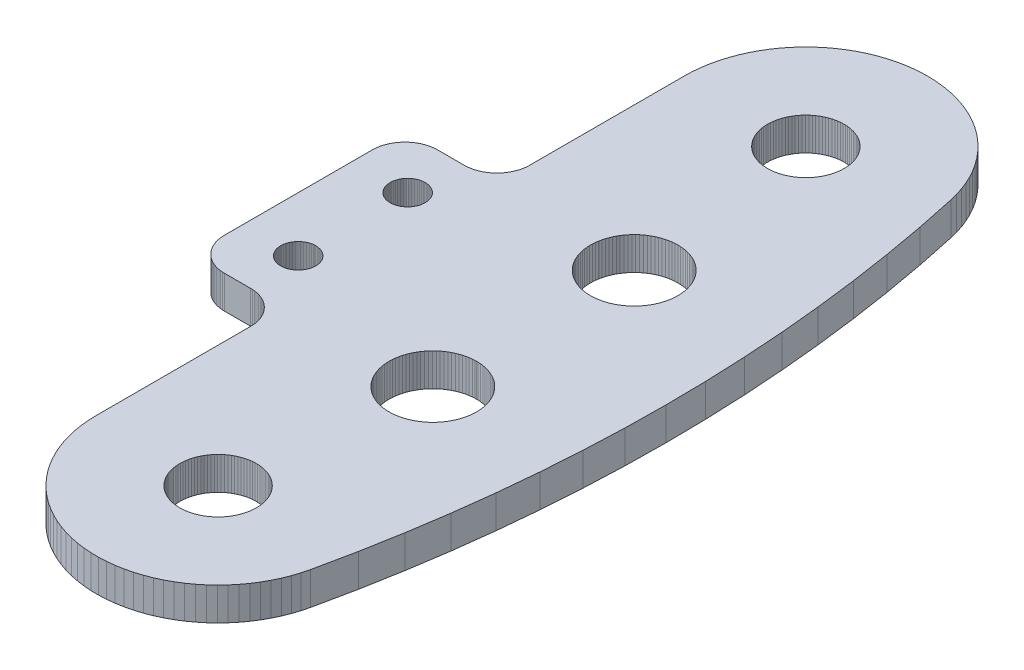
SolidWorks part; units mm, degrees
ref_plane "Front Plane" through (0, 0, 0) normal (0, 0, 1) x (1, 0, 0)
ref_plane "Top Plane" through (0, 0, 0) normal (0, 1, 0) x (1, 0, 0)
ref_plane "Right Plane" through (0, 0, 0) normal (1, 0, 0) x (0, 0, -1)
ref_plane "Plane1" through (0, 3, 0) normal (0, 1, 0) x (1, 0, 0)
sketch "Sketch1" plane through (0, 3, 0) normal (0, 1, 0) x (1, 0, 0)
  line L0 (19.864, -7.6394) -> (20.0843, -7.6675)
  line L1 (20.0843, -7.6675) -> (20.3023, -7.7095)
  line L2 (20.3023, -7.7095) -> (20.5173, -7.7653)
  line L3 (20.5173, -7.7653) -> (20.7283, -7.8346)
  line L4 (20.7283, -7.8346) -> (20.9345, -7.9171)
  line L5 (20.9345, -7.9171) -> (21.1351, -8.0126)
  line L6 (21.1351, -8.0126) -> (21.3291, -8.1206)
  line L7 (21.3291, -8.1206) -> (21.516, -8.2407)
  line L8 (21.516, -8.2407) -> (21.6948, -8.3723)
  line L9 (21.6948, -8.3723) -> (21.865, -8.5151)
  line L10 (21.865, -8.5151) -> (22.0257, -8.6684)
  line L11 (22.0257, -8.6684) -> (22.1764, -8.8315)
  line L12 (22.1764, -8.8315) -> (22.3164, -9.0039)
  line L13 (22.3164, -9.0039) -> (22.4453, -9.1848)
  line L14 (22.4453, -9.1848) -> (22.5623, -9.3735)
  line L15 (22.5623, -9.3735) -> (22.6672, -9.5693)
  line L16 (22.6672, -9.5693) -> (22.7595, -9.7713)
  line L17 (22.7595, -9.7713) -> (22.8388, -9.9788)
  line L18 (22.8388, -9.9788) -> (22.9047, -10.1909)
  line L19 (22.9047, -10.1909) -> (22.9571, -10.4067)
  line L20 (22.9571, -10.4067) -> (22.9956, -10.6254)
  line L21 (22.9956, -10.6254) -> (23.0203, -10.8461)
  line L22 (23.0203, -10.8461) -> (23.0308, -11.068)
  line L23 (23.0308, -11.068) -> (23.0273, -11.2901)
  line L24 (23.0273, -11.2901) -> (23.0097, -11.5115)
  line L25 (23.0097, -11.5115) -> (22.9781, -11.7314)
  line L26 (22.9781, -11.7314) -> (22.9326, -11.9487)
  line L27 (22.9326, -11.9487) -> (22.8734, -12.1628)
  line L28 (22.8734, -12.1628) -> (22.8008, -12.3727)
  line L29 (22.8008, -12.3727) -> (22.715, -12.5775)
  line L30 (22.715, -12.5775) -> (22.6164, -12.7765)
  line L31 (22.6164, -12.7765) -> (22.5053, -12.9689)
  line L32 (22.5053, -12.9689) -> (22.3823, -13.1538)
  line L33 (22.3823, -13.1538) -> (22.2478, -13.3305)
  line L34 (22.2478, -13.3305) -> (22.1023, -13.4984)
  line L35 (22.1023, -13.4984) -> (21.9466, -13.6567)
  line L36 (21.9466, -13.6567) -> (21.781, -13.8047)
  line L37 (21.781, -13.8047) -> (21.6065, -13.942)
  line L38 (21.6065, -13.942) -> (21.4235, -14.068)
  line L39 (21.4235, -14.068) -> (21.233, -14.1821)
  line L40 (21.233, -14.1821) -> (21.0356, -14.2838)
  line L41 (21.0356, -14.2838) -> (20.8321, -14.3729)
  line L42 (20.8321, -14.3729) -> (20.6234, -14.4488)
  line L43 (20.6234, -14.4488) -> (20.4103, -14.5114)
  line L44 (20.4103, -14.5114) -> (20.1936, -14.5603)
  line L45 (20.1936, -14.5603) -> (19.9743, -14.5954)
  line L46 (19.9743, -14.5954) -> (19.7533, -14.6165)
  line L47 (19.7533, -14.6165) -> (19.5313, -14.6236)
  line L48 (19.5313, -14.6236) -> (19.3093, -14.6165)
  line L49 (19.3093, -14.6165) -> (19.0882, -14.5954)
  line L50 (19.0882, -14.5954) -> (18.8689, -14.5603)
  line L51 (18.8689, -14.5603) -> (18.6523, -14.5114)
  line L52 (18.6523, -14.5114) -> (18.4392, -14.4488)
  line L53 (18.4392, -14.4488) -> (18.2305, -14.3728)
  line L54 (18.2305, -14.3728) -> (18.027, -14.2838)
  line L55 (18.027, -14.2838) -> (17.8296, -14.182)
  line L56 (17.8296, -14.182) -> (17.639, -14.0679)
  line L57 (17.639, -14.0679) -> (17.4561, -13.942)
  line L58 (17.4561, -13.942) -> (17.2815, -13.8047)
  line L59 (17.2815, -13.8047) -> (17.116, -13.6566)
  line L60 (17.116, -13.6566) -> (16.9602, -13.4983)
  line L61 (16.9602, -13.4983) -> (16.8148, -13.3305)
  line L62 (16.8148, -13.3305) -> (16.7656, -13.2659)
  line L63 (16.7656, -13.2659) -> (16.6803, -13.1538)
  line L64 (16.6803, -13.1538) -> (16.5572, -12.9688)
  line L65 (16.5572, -12.9688) -> (16.4462, -12.7765)
  line L66 (16.4462, -12.7765) -> (16.3476, -12.5775)
  line L67 (16.3476, -12.5775) -> (16.2618, -12.3727)
  line L68 (16.2618, -12.3727) -> (16.1891, -12.1628)
  line L69 (16.1891, -12.1628) -> (16.1299, -11.9487)
  line L70 (16.1299, -11.9487) -> (16.0844, -11.7313)
  line L71 (16.0844, -11.7313) -> (16.0528, -11.5115)
  line L72 (16.0528, -11.5115) -> (16.0352, -11.2901)
  line L73 (16.0352, -11.2901) -> (16.0317, -11.068)
  line L74 (16.0317, -11.068) -> (16.0423, -10.8462)
  line L75 (16.0423, -10.8462) -> (16.0669, -10.6254)
  line L76 (16.0669, -10.6254) -> (16.1055, -10.4067)
  line L77 (16.1055, -10.4067) -> (16.1578, -10.1909)
  line L78 (16.1578, -10.1909) -> (16.2238, -9.9788)
  line L79 (16.2238, -9.9788) -> (16.303, -9.7713)
  line L80 (16.303, -9.7713) -> (16.3953, -9.5693)
  line L81 (16.3953, -9.5693) -> (16.5002, -9.3736)
  line L82 (16.5002, -9.3736) -> (16.6173, -9.1848)
  line L83 (16.6173, -9.1848) -> (16.7461, -9.0039)
  line L84 (16.7461, -9.0039) -> (16.7656, -8.9799)
  line L85 (16.7656, -8.9799) -> (16.8862, -8.8315)
  line L86 (16.8862, -8.8315) -> (17.0368, -8.6684)
  line L87 (17.0368, -8.6684) -> (17.1976, -8.5151)
  line L88 (17.1976, -8.5151) -> (17.3677, -8.3724)
  line L89 (17.3677, -8.3724) -> (17.5466, -8.2407)
  line L90 (17.5466, -8.2407) -> (17.7334, -8.1206)
  line L91 (17.7334, -8.1206) -> (17.9275, -8.0126)
  line L92 (17.9275, -8.0126) -> (18.128, -7.9172)
  line L93 (18.128, -7.9172) -> (18.3342, -7.8346)
  line L94 (18.3342, -7.8346) -> (18.5452, -7.7653)
  line L95 (18.5452, -7.7653) -> (18.7602, -7.7095)
  line L96 (18.7602, -7.7095) -> (18.9783, -7.6675)
  line L97 (18.9783, -7.6675) -> (19.1986, -7.6394)
  line L98 (19.1986, -7.6394) -> (19.4202, -7.6253)
  line L99 (19.4202, -7.6253) -> (19.6423, -7.6253)
  line L100 (19.6423, -7.6253) -> (19.864, -7.6394)
  line L101 (3.8959, -31.817) -> (3.9715, -31.7493)
  line L102 (3.9715, -31.7493) -> (4.0513, -31.6866)
  line L103 (4.0513, -31.6866) -> (4.135, -31.629)
  line L104 (4.135, -31.629) -> (4.2221, -31.5768)
  line L105 (4.2221, -31.5768) -> (4.3123, -31.5303)
  line L106 (4.3123, -31.5303) -> (4.4053, -31.4896)
  line L107 (4.4053, -31.4896) -> (4.5007, -31.4549)
  line L108 (4.5007, -31.4549) -> (4.5982, -31.4263)
  line L109 (4.5982, -31.4263) -> (4.6972, -31.4039)
  line L110 (4.6972, -31.4039) -> (4.7975, -31.3879)
  line L111 (4.7975, -31.3879) -> (4.8985, -31.3782)
  line L112 (4.8985, -31.3782) -> (5, -31.375)
  line L113 (5, -31.375) -> (5.1015, -31.3782)
  line L114 (5.1015, -31.3782) -> (5.2025, -31.3879)
  line L115 (5.2025, -31.3879) -> (5.3028, -31.4039)
  line L116 (5.3028, -31.4039) -> (5.4018, -31.4263)
  line L117 (5.4018, -31.4263) -> (5.4993, -31.4549)
  line L118 (5.4993, -31.4549) -> (5.5947, -31.4896)
  line L119 (5.5947, -31.4896) -> (5.6877, -31.5303)
  line L120 (5.6877, -31.5303) -> (5.7779, -31.5768)
  line L121 (5.7779, -31.5768) -> (5.865, -31.629)
  line L122 (5.865, -31.629) -> (5.9487, -31.6866)
  line L123 (5.9487, -31.6866) -> (6.0285, -31.7493)
  line L124 (6.0285, -31.7493) -> (6.1041, -31.817)
  line L125 (6.1041, -31.817) -> (6.1753, -31.8894)
  line L126 (6.1753, -31.8894) -> (6.2418, -31.9661)
  line L127 (6.2418, -31.9661) -> (6.3033, -32.0469)
  line L128 (6.3033, -32.0469) -> (6.3596, -32.1314)
  line L129 (6.3596, -32.1314) -> (6.4103, -32.2194)
  line L130 (6.4103, -32.2194) -> (6.4554, -32.3103)
  line L131 (6.4554, -32.3103) -> (6.4946, -32.404)
  line L132 (6.4946, -32.404) -> (6.5278, -32.4999)
  line L133 (6.5278, -32.4999) -> (6.5549, -32.5978)
  line L134 (6.5549, -32.5978) -> (6.5757, -32.6972)
  line L135 (6.5757, -32.6972) -> (6.5901, -32.7977)
  line L136 (6.5901, -32.7977) -> (6.5982, -32.8989)
  line L137 (6.5982, -32.8989) -> (6.5998, -33.0004)
  line L138 (6.5998, -33.0004) -> (6.595, -33.1018)
  line L139 (6.595, -33.1018) -> (6.5837, -33.2027)
  line L140 (6.5837, -33.2027) -> (6.5661, -33.3027)
  line L141 (6.5661, -33.3027) -> (6.5421, -33.4014)
  line L142 (6.5421, -33.4014) -> (6.512, -33.4983)
  line L143 (6.512, -33.4983) -> (6.4758, -33.5932)
  line L144 (6.4758, -33.5932) -> (6.4336, -33.6855)
  line L145 (6.4336, -33.6855) -> (6.3856, -33.775)
  line L146 (6.3856, -33.775) -> (6.3321, -33.8613)
  line L147 (6.3321, -33.8613) -> (6.2732, -33.944)
  line L148 (6.2732, -33.944) -> (6.2092, -34.0228)
  line L149 (6.2092, -34.0228) -> (6.1403, -34.0974)
  line L150 (6.1403, -34.0974) -> (6.0668, -34.1674)
  line L151 (6.0668, -34.1674) -> (5.9891, -34.2327)
  line L152 (5.9891, -34.2327) -> (5.9073, -34.2929)
  line L153 (5.9073, -34.2929) -> (5.8219, -34.3478)
  line L154 (5.8219, -34.3478) -> (5.7332, -34.3971)
  line L155 (5.7332, -34.3971) -> (5.6415, -34.4408)
  line L156 (5.6415, -34.4408) -> (5.5472, -34.4785)
  line L157 (5.5472, -34.4785) -> (5.4508, -34.5102)
  line L158 (5.4508, -34.5102) -> (5.3525, -34.5357)
  line L159 (5.3525, -34.5357) -> (5.2528, -34.5549)
  line L160 (5.2528, -34.5549) -> (5.1521, -34.5678)
  line L161 (5.1521, -34.5678) -> (5.0508, -34.5742)
  line L162 (5.0508, -34.5742) -> (5, -34.575)
  line L163 (5, -34.575) -> (4.9492, -34.5742)
  line L164 (4.9492, -34.5742) -> (4.8479, -34.5678)
  line L165 (4.8479, -34.5678) -> (4.7472, -34.5549)
  line L166 (4.7472, -34.5549) -> (4.6475, -34.5357)
  line L167 (4.6475, -34.5357) -> (4.5492, -34.5102)
  line L168 (4.5492, -34.5102) -> (4.4528, -34.4785)
  line L169 (4.4528, -34.4785) -> (4.3585, -34.4408)
  line L170 (4.3585, -34.4408) -> (4.2668, -34.3971)
  line L171 (4.2668, -34.3971) -> (4.1781, -34.3478)
  line L172 (4.1781, -34.3478) -> (4.0927, -34.2929)
  line L173 (4.0927, -34.2929) -> (4.0109, -34.2327)
  line L174 (4.0109, -34.2327) -> (3.9332, -34.1674)
  line L175 (3.9332, -34.1674) -> (3.8597, -34.0974)
  line L176 (3.8597, -34.0974) -> (3.7908, -34.0228)
  line L177 (3.7908, -34.0228) -> (3.7268, -33.944)
  line L178 (3.7268, -33.944) -> (3.6679, -33.8613)
  line L179 (3.6679, -33.8613) -> (3.6144, -33.775)
  line L180 (3.6144, -33.775) -> (3.5664, -33.6855)
  line L181 (3.5664, -33.6855) -> (3.5242, -33.5932)
  line L182 (3.5242, -33.5932) -> (3.488, -33.4983)
  line L183 (3.488, -33.4983) -> (3.4579, -33.4014)
  line L184 (3.4579, -33.4014) -> (3.4339, -33.3027)
  line L185 (3.4339, -33.3027) -> (3.4163, -33.2027)
  line L186 (3.4163, -33.2027) -> (3.405, -33.1018)
  line L187 (3.405, -33.1018) -> (3.4002, -33.0004)
  line L188 (3.4002, -33.0004) -> (3.4018, -32.8989)
  line L189 (3.4018, -32.8989) -> (3.4099, -32.7977)
  line L190 (3.4099, -32.7977) -> (3.4243, -32.6972)
  line L191 (3.4243, -32.6972) -> (3.4451, -32.5978)
  line L192 (3.4451, -32.5978) -> (3.4722, -32.4999)
  line L193 (3.4722, -32.4999) -> (3.5054, -32.404)
  line L194 (3.5054, -32.404) -> (3.5446, -32.3103)
  line L195 (3.5446, -32.3103) -> (3.5897, -32.2194)
  line L196 (3.5897, -32.2194) -> (3.6404, -32.1314)
  line L197 (3.6404, -32.1314) -> (3.6967, -32.0469)
  line L198 (3.6967, -32.0469) -> (3.7582, -31.9661)
  line L199 (3.7582, -31.9661) -> (3.8247, -31.8894)
  line L200 (3.8247, -31.8894) -> (3.8959, -31.817)
  line L201 (3.7268, -43.944) -> (3.6679, -43.8613)
  line L202 (3.6679, -43.8613) -> (3.6144, -43.775)
  line L203 (3.6144, -43.775) -> (3.5664, -43.6855)
  line L204 (3.5664, -43.6855) -> (3.5242, -43.5932)
  line L205 (3.5242, -43.5932) -> (3.488, -43.4983)
  line L206 (3.488, -43.4983) -> (3.4579, -43.4014)
  line L207 (3.4579, -43.4014) -> (3.4339, -43.3027)
  line L208 (3.4339, -43.3027) -> (3.4163, -43.2027)
  line L209 (3.4163, -43.2027) -> (3.405, -43.1018)
  line L210 (3.405, -43.1018) -> (3.4002, -43.0004)
  line L211 (3.4002, -43.0004) -> (3.4018, -42.8989)
  line L212 (3.4018, -42.8989) -> (3.4099, -42.7977)
  line L213 (3.4099, -42.7977) -> (3.4243, -42.6972)
  line L214 (3.4243, -42.6972) -> (3.4451, -42.5978)
  line L215 (3.4451, -42.5978) -> (3.4722, -42.4999)
  line L216 (3.4722, -42.4999) -> (3.5054, -42.404)
  line L217 (3.5054, -42.404) -> (3.5446, -42.3103)
  line L218 (3.5446, -42.3103) -> (3.5621, -42.275)
  line L219 (3.5621, -42.275) -> (3.5897, -42.2194)
  line L220 (3.5897, -42.2194) -> (3.6404, -42.1315)
  line L221 (3.6404, -42.1315) -> (3.6967, -42.0469)
  line L222 (3.6967, -42.0469) -> (3.7582, -41.9661)
  line L223 (3.7582, -41.9661) -> (3.8247, -41.8894)
  line L224 (3.8247, -41.8894) -> (3.8959, -41.8171)
  line L225 (3.8959, -41.8171) -> (3.9716, -41.7494)
  line L226 (3.9716, -41.7494) -> (4.0514, -41.6866)
  line L227 (4.0514, -41.6866) -> (4.135, -41.629)
  line L228 (4.135, -41.629) -> (4.2221, -41.5769)
  line L229 (4.2221, -41.5769) -> (4.3124, -41.5304)
  line L230 (4.3124, -41.5304) -> (4.4054, -41.4897)
  line L231 (4.4054, -41.4897) -> (4.5008, -41.4549)
  line L232 (4.5008, -41.4549) -> (4.5982, -41.4263)
  line L233 (4.5982, -41.4263) -> (4.6972, -41.404)
  line L234 (4.6972, -41.404) -> (4.7975, -41.3879)
  line L235 (4.7975, -41.3879) -> (4.8986, -41.3783)
  line L236 (4.8986, -41.3783) -> (5, -41.3751)
  line L237 (5, -41.3751) -> (5.1015, -41.3783)
  line L238 (5.1015, -41.3783) -> (5.2026, -41.388)
  line L239 (5.2026, -41.388) -> (5.3028, -41.404)
  line L240 (5.3028, -41.404) -> (5.4019, -41.4264)
  line L241 (5.4019, -41.4264) -> (5.4993, -41.455)
  line L242 (5.4993, -41.455) -> (5.5947, -41.4897)
  line L243 (5.5947, -41.4897) -> (5.6877, -41.5304)
  line L244 (5.6877, -41.5304) -> (5.7779, -41.577)
  line L245 (5.7779, -41.577) -> (5.8651, -41.6291)
  line L246 (5.8651, -41.6291) -> (5.9487, -41.6867)
  line L247 (5.9487, -41.6867) -> (6.0285, -41.7495)
  line L248 (6.0285, -41.7495) -> (6.1041, -41.8172)
  line L249 (6.1041, -41.8172) -> (6.1754, -41.8895)
  line L250 (6.1754, -41.8895) -> (6.2418, -41.9662)
  line L251 (6.2418, -41.9662) -> (6.3033, -42.047)
  line L252 (6.3033, -42.047) -> (6.3596, -42.1316)
  line L253 (6.3596, -42.1316) -> (6.4103, -42.2195)
  line L254 (6.4103, -42.2195) -> (6.4379, -42.2751)
  line L255 (6.4379, -42.2751) -> (6.4554, -42.3105)
  line L256 (6.4554, -42.3105) -> (6.4946, -42.4041)
  line L257 (6.4946, -42.4041) -> (6.5278, -42.5001)
  line L258 (6.5278, -42.5001) -> (6.5549, -42.5979)
  line L259 (6.5549, -42.5979) -> (6.5757, -42.6973)
  line L260 (6.5757, -42.6973) -> (6.5901, -42.7978)
  line L261 (6.5901, -42.7978) -> (6.5981, -42.899)
  line L262 (6.5981, -42.899) -> (6.5997, -43.0005)
  line L263 (6.5997, -43.0005) -> (6.595, -43.1018)
  line L264 (6.595, -43.1018) -> (6.5837, -43.2027)
  line L265 (6.5837, -43.2027) -> (6.5661, -43.3027)
  line L266 (6.5661, -43.3027) -> (6.5421, -43.4014)
  line L267 (6.5421, -43.4014) -> (6.512, -43.4983)
  line L268 (6.512, -43.4983) -> (6.4758, -43.5932)
  line L269 (6.4758, -43.5932) -> (6.4336, -43.6855)
  line L270 (6.4336, -43.6855) -> (6.3856, -43.775)
  line L271 (6.3856, -43.775) -> (6.3321, -43.8613)
  line L272 (6.3321, -43.8613) -> (6.2732, -43.944)
  line L273 (6.2732, -43.944) -> (6.2092, -44.0228)
  line L274 (6.2092, -44.0228) -> (6.1403, -44.0974)
  line L275 (6.1403, -44.0974) -> (6.0668, -44.1674)
  line L276 (6.0668, -44.1674) -> (5.9891, -44.2327)
  line L277 (5.9891, -44.2327) -> (5.9073, -44.2929)
  line L278 (5.9073, -44.2929) -> (5.8219, -44.3478)
  line L279 (5.8219, -44.3478) -> (5.7332, -44.3971)
  line L280 (5.7332, -44.3971) -> (5.6415, -44.4408)
  line L281 (5.6415, -44.4408) -> (5.5472, -44.4785)
  line L282 (5.5472, -44.4785) -> (5.4508, -44.5102)
  line L283 (5.4508, -44.5102) -> (5.3525, -44.5357)
  line L284 (5.3525, -44.5357) -> (5.2528, -44.5549)
  line L285 (5.2528, -44.5549) -> (5.1521, -44.5678)
  line L286 (5.1521, -44.5678) -> (5.0508, -44.5742)
  line L287 (5.0508, -44.5742) -> (5, -44.575)
  line L288 (5, -44.575) -> (4.9492, -44.5742)
  line L289 (4.9492, -44.5742) -> (4.8479, -44.5678)
  line L290 (4.8479, -44.5678) -> (4.7472, -44.5549)
  line L291 (4.7472, -44.5549) -> (4.6475, -44.5357)
  line L292 (4.6475, -44.5357) -> (4.5492, -44.5102)
  line L293 (4.5492, -44.5102) -> (4.4528, -44.4785)
  line L294 (4.4528, -44.4785) -> (4.3585, -44.4408)
  line L295 (4.3585, -44.4408) -> (4.2668, -44.3971)
  line L296 (4.2668, -44.3971) -> (4.1781, -44.3478)
  line L297 (4.1781, -44.3478) -> (4.0927, -44.2929)
  line L298 (4.0927, -44.2929) -> (4.0109, -44.2327)
  line L299 (4.0109, -44.2327) -> (3.9332, -44.1674)
  line L300 (3.9332, -44.1674) -> (3.8597, -44.0974)
  line L301 (3.8597, -44.0974) -> (3.7908, -44.0228)
  line L302 (3.7908, -44.0228) -> (3.7268, -43.944)
  line L303 (19.7298, -0.0017) -> (19.0231, -0.0116)
  line L304 (19.0231, -0.0116) -> (18.3185, -0.0663)
  line L305 (18.3185, -0.0663) -> (17.6188, -0.1656)
  line L306 (17.6188, -0.1656) -> (16.9268, -0.3092)
  line L307 (16.9268, -0.3092) -> (16.7656, -0.3535)
  line L308 (16.7656, -0.3535) -> (16.2453, -0.4964)
  line L309 (16.2453, -0.4964) -> (15.5771, -0.7266)
  line L310 (15.5771, -0.7266) -> (14.9248, -0.9986)
  line L311 (14.9248, -0.9986) -> (14.2911, -1.3116)
  line L312 (14.2911, -1.3116) -> (13.6786, -1.6642)
  line L313 (13.6786, -1.6642) -> (13.0897, -2.0549)
  line L314 (13.0897, -2.0549) -> (12.5269, -2.4823)
  line L315 (12.5269, -2.4823) -> (11.9922, -2.9445)
  line L316 (11.9922, -2.9445) -> (11.4881, -3.4398)
  line L317 (11.4881, -3.4398) -> (11.3156, -3.6322)
  line L318 (11.3156, -3.6322) -> (11.1547, -3.8118)
  line L319 (11.1547, -3.8118) -> (11.0164, -3.9661)
  line L320 (11.0164, -3.9661) -> (10.579, -4.5212)
  line L321 (10.579, -4.5212) -> (10.1778, -5.103)
  line L322 (10.1778, -5.103) -> (9.8144, -5.7092)
  line L323 (9.8144, -5.7092) -> (9.4902, -6.3371)
  line L324 (9.4902, -6.3371) -> (9.2065, -6.9844)
  line L325 (9.2065, -6.9844) -> (8.9645, -7.6485)
  line L326 (8.9645, -7.6485) -> (8.7651, -8.3265)
  line L327 (8.7651, -8.3265) -> (8.6092, -9.0158)
  line L328 (8.6092, -9.0158) -> (8.4974, -9.7136)
  line L329 (8.4974, -9.7136) -> (8.4302, -10.4172)
  line L330 (8.4302, -10.4172) -> (8.4077, -11.1236)
  line L331 (8.4077, -11.1236) -> (8.4077, -25.1236)
  line L332 (8.4077, -25.1236) -> (8.4083, -25.3087)
  line L333 (8.4083, -25.3087) -> (8.3974, -25.4935)
  line L334 (8.3974, -25.4935) -> (8.3752, -25.6772)
  line L335 (8.3752, -25.6772) -> (8.3416, -25.8593)
  line L336 (8.3416, -25.8593) -> (8.2969, -26.0389)
  line L337 (8.2969, -26.0389) -> (8.2412, -26.2155)
  line L338 (8.2412, -26.2155) -> (8.1747, -26.3883)
  line L339 (8.1747, -26.3883) -> (8.0977, -26.5566)
  line L340 (8.0977, -26.5566) -> (8.0105, -26.7199)
  line L341 (8.0105, -26.7199) -> (7.9133, -26.8774)
  line L342 (7.9133, -26.8774) -> (7.8066, -27.0287)
  line L343 (7.8066, -27.0287) -> (7.6908, -27.1732)
  line L344 (7.6908, -27.1732) -> (7.5663, -27.3102)
  line L345 (7.5663, -27.3102) -> (7.4336, -27.4392)
  line L346 (7.4336, -27.4392) -> (7.2932, -27.5598)
  line L347 (7.2932, -27.5598) -> (7.1456, -27.6716)
  line L348 (7.1456, -27.6716) -> (6.9914, -27.774)
  line L349 (6.9914, -27.774) -> (6.8312, -27.8667)
  line L350 (6.8312, -27.8667) -> (6.6655, -27.9494)
  line L351 (6.6655, -27.9494) -> (6.4951, -28.0217)
  line L352 (6.4951, -28.0217) -> (6.3206, -28.0833)
  line L353 (6.3206, -28.0833) -> (6.1425, -28.1341)
  line L354 (6.1425, -28.1341) -> (5.9617, -28.1737)
  line L355 (5.9617, -28.1737) -> (5.7788, -28.2022)
  line L356 (5.7788, -28.2022) -> (5.5945, -28.2193)
  line L357 (5.5945, -28.2193) -> (5.4094, -28.225)
  line L358 (5.4094, -28.225) -> (3, -28.225)
  line L359 (3, -28.225) -> (2.8116, -28.2309)
  line L360 (2.8116, -28.2309) -> (2.624, -28.2487)
  line L361 (2.624, -28.2487) -> (2.4379, -28.2781)
  line L362 (2.4379, -28.2781) -> (2.2539, -28.3193)
  line L363 (2.2539, -28.3193) -> (2.0729, -28.3718)
  line L364 (2.0729, -28.3718) -> (1.8956, -28.4357)
  line L365 (1.8956, -28.4357) -> (1.7227, -28.5105)
  line L366 (1.7227, -28.5105) -> (1.5547, -28.5961)
  line L367 (1.5547, -28.5961) -> (1.3925, -28.692)
  line L368 (1.3925, -28.692) -> (1.2366, -28.798)
  line L369 (1.2366, -28.798) -> (1.0877, -28.9135)
  line L370 (1.0877, -28.9135) -> (0.9464, -29.0381)
  line L371 (0.9464, -29.0381) -> (0.8131, -29.1714)
  line L372 (0.8131, -29.1714) -> (0.6885, -29.3127)
  line L373 (0.6885, -29.3127) -> (0.5729, -29.4617)
  line L374 (0.5729, -29.4617) -> (0.467, -29.6175)
  line L375 (0.467, -29.6175) -> (0.3711, -29.7797)
  line L376 (0.3711, -29.7797) -> (0.2855, -29.9477)
  line L377 (0.2855, -29.9477) -> (0.2107, -30.1206)
  line L378 (0.2107, -30.1206) -> (0.1468, -30.298)
  line L379 (0.1468, -30.298) -> (0.0943, -30.4789)
  line L380 (0.0943, -30.4789) -> (0.0531, -30.6629)
  line L381 (0.0531, -30.6629) -> (0.0237, -30.849)
  line L382 (0.0237, -30.849) -> (0.0059, -31.0366)
  line L383 (0.0059, -31.0366) -> (0, -31.225)
  line L384 (0, -31.225) -> (0, -44.725)
  line L385 (0, -44.725) -> (0.0059, -44.9134)
  line L386 (0.0059, -44.9134) -> (0.0237, -45.101)
  line L387 (0.0237, -45.101) -> (0.0531, -45.2872)
  line L388 (0.0531, -45.2872) -> (0.0943, -45.4711)
  line L389 (0.0943, -45.4711) -> (0.1468, -45.6521)
  line L390 (0.1468, -45.6521) -> (0.2107, -45.8294)
  line L391 (0.2107, -45.8294) -> (0.2855, -46.0023)
  line L392 (0.2855, -46.0023) -> (0.3711, -46.1703)
  line L393 (0.3711, -46.1703) -> (0.467, -46.3325)
  line L394 (0.467, -46.3325) -> (0.5729, -46.4884)
  line L395 (0.5729, -46.4884) -> (0.6885, -46.6373)
  line L396 (0.6885, -46.6373) -> (0.8131, -46.7786)
  line L397 (0.8131, -46.7786) -> (0.9464, -46.9119)
  line L398 (0.9464, -46.9119) -> (1.0877, -47.0366)
  line L399 (1.0877, -47.0366) -> (1.2366, -47.1521)
  line L400 (1.2366, -47.1521) -> (1.3925, -47.258)
  line L401 (1.3925, -47.258) -> (1.5547, -47.3539)
  line L402 (1.5547, -47.3539) -> (1.7227, -47.4395)
  line L403 (1.7227, -47.4395) -> (1.8956, -47.5143)
  line L404 (1.8956, -47.5143) -> (2.0729, -47.5782)
  line L405 (2.0729, -47.5782) -> (2.2539, -47.6308)
  line L406 (2.2539, -47.6308) -> (2.4379, -47.6719)
  line L407 (2.4379, -47.6719) -> (2.624, -47.7014)
  line L408 (2.624, -47.7014) -> (2.8116, -47.7191)
  line L409 (2.8116, -47.7191) -> (3, -47.725)
  line L410 (3, -47.725) -> (5.4094, -47.725)
  line L411 (5.4094, -47.725) -> (5.5945, -47.7307)
  line L412 (5.5945, -47.7307) -> (5.7788, -47.7478)
  line L413 (5.7788, -47.7478) -> (5.9617, -47.7763)
  line L414 (5.9617, -47.7763) -> (6.1425, -47.816)
  line L415 (6.1425, -47.816) -> (6.3206, -47.8667)
  line L416 (6.3206, -47.8667) -> (6.4951, -47.9283)
  line L417 (6.4951, -47.9283) -> (6.6655, -48.0006)
  line L418 (6.6655, -48.0006) -> (6.8312, -48.0833)
  line L419 (6.8312, -48.0833) -> (6.9914, -48.176)
  line L420 (6.9914, -48.176) -> (7.1456, -48.2784)
  line L421 (7.1456, -48.2784) -> (7.2932, -48.3902)
  line L422 (7.2932, -48.3902) -> (7.4336, -48.5108)
  line L423 (7.4336, -48.5108) -> (7.5663, -48.6399)
  line L424 (7.5663, -48.6399) -> (7.6908, -48.7769)
  line L425 (7.6908, -48.7769) -> (7.8066, -48.9213)
  line L426 (7.8066, -48.9213) -> (7.9133, -49.0726)
  line L427 (7.9133, -49.0726) -> (8.0105, -49.2302)
  line L428 (8.0105, -49.2302) -> (8.0977, -49.3934)
  line L429 (8.0977, -49.3934) -> (8.1747, -49.5618)
  line L430 (8.1747, -49.5618) -> (8.2412, -49.7345)
  line L431 (8.2412, -49.7345) -> (8.2969, -49.9111)
  line L432 (8.2969, -49.9111) -> (8.3416, -50.0907)
  line L433 (8.3416, -50.0907) -> (8.3752, -50.2728)
  line L434 (8.3752, -50.2728) -> (8.3974, -50.4565)
  line L435 (8.3974, -50.4565) -> (8.4083, -50.6414)
  line L436 (8.4083, -50.6414) -> (8.4077, -50.8265)
  line L437 (8.4077, -50.8265) -> (8.4077, -64.8265)
  line L438 (8.4077, -64.8265) -> (8.4302, -65.5328)
  line L439 (8.4302, -65.5328) -> (8.4974, -66.2364)
  line L440 (8.4974, -66.2364) -> (8.6092, -66.9342)
  line L441 (8.6092, -66.9342) -> (8.7651, -67.6235)
  line L442 (8.7651, -67.6235) -> (8.9645, -68.3016)
  line L443 (8.9645, -68.3016) -> (9.2065, -68.9656)
  line L444 (9.2065, -68.9656) -> (9.4902, -69.6129)
  line L445 (9.4902, -69.6129) -> (9.8144, -70.2409)
  line L446 (9.8144, -70.2409) -> (10.1778, -70.847)
  line L447 (10.1778, -70.847) -> (10.579, -71.4288)
  line L448 (10.579, -71.4288) -> (11.0164, -71.984)
  line L449 (11.0164, -71.984) -> (11.4881, -72.5102)
  line L450 (11.4881, -72.5102) -> (11.9922, -73.0055)
  line L451 (11.9922, -73.0055) -> (12.5269, -73.4677)
  line L452 (12.5269, -73.4677) -> (13.0897, -73.8951)
  line L453 (13.0897, -73.8951) -> (13.6786, -74.2858)
  line L454 (13.6786, -74.2858) -> (14.2911, -74.6384)
  line L455 (14.2911, -74.6384) -> (14.9248, -74.9514)
  line L456 (14.9248, -74.9514) -> (15.5771, -75.2235)
  line L457 (15.5771, -75.2235) -> (16.2453, -75.4536)
  line L458 (16.2453, -75.4536) -> (16.7656, -75.5965)
  line L459 (16.7656, -75.5965) -> (16.9268, -75.6408)
  line L460 (16.9268, -75.6408) -> (17.6188, -75.7844)
  line L461 (17.6188, -75.7844) -> (18.3185, -75.8837)
  line L462 (18.3185, -75.8837) -> (19.0231, -75.9384)
  line L463 (19.0231, -75.9384) -> (19.7298, -75.9483)
  line L464 (19.7298, -75.9483) -> (20.4356, -75.9132)
  line L465 (20.4356, -75.9132) -> (21.1378, -75.8334)
  line L466 (21.1378, -75.8334) -> (21.8336, -75.7092)
  line L467 (21.8336, -75.7092) -> (22.52, -75.5411)
  line L468 (22.52, -75.5411) -> (23.1944, -75.3296)
  line L469 (23.1944, -75.3296) -> (23.854, -75.0758)
  line L470 (23.854, -75.0758) -> (24.2656, -74.8866)
  line L471 (24.2656, -74.8866) -> (24.4961, -74.7807)
  line L472 (24.4961, -74.7807) -> (25.1182, -74.4453)
  line L473 (25.1182, -74.4453) -> (25.7177, -74.0711)
  line L474 (25.7177, -74.0711) -> (26.2923, -73.6595)
  line L475 (26.2923, -73.6595) -> (26.8395, -73.2123)
  line L476 (26.8395, -73.2123) -> (27.3573, -72.7313)
  line L477 (27.3573, -72.7313) -> (27.8435, -72.2184)
  line L478 (27.8435, -72.2184) -> (28.2961, -71.6756)
  line L479 (28.2961, -71.6756) -> (28.7133, -71.1052)
  line L480 (28.7133, -71.1052) -> (29.0935, -70.5094)
  line L481 (29.0935, -70.5094) -> (29.4351, -69.8907)
  line L482 (29.4351, -69.8907) -> (29.7367, -69.2515)
  line L483 (29.7367, -69.2515) -> (29.9971, -68.5945)
  line L484 (29.9971, -68.5945) -> (30.2152, -67.9223)
  line L485 (30.2152, -67.9223) -> (30.3902, -67.2376)
  line L486 (30.3902, -67.2376) -> (31.1401, -63.6277)
  line L487 (31.1401, -63.6277) -> (31.7912, -59.9986)
  line L488 (31.7912, -59.9986) -> (32.3428, -56.3532)
  line L489 (32.3428, -56.3532) -> (32.3555, -56.2507)
  line L490 (32.3555, -56.2507) -> (32.7949, -52.694)
  line L491 (32.7949, -52.694) -> (33.1468, -49.0238)
  line L492 (33.1468, -49.0238) -> (33.3984, -45.3455)
  line L493 (33.3984, -45.3455) -> (33.5243, -42.2749)
  line L494 (33.5243, -42.2749) -> (33.5494, -41.6616)
  line L495 (33.5494, -41.6616) -> (33.5998, -37.9749)
  line L496 (33.5998, -37.9749) -> (33.5494, -34.2884)
  line L497 (33.5494, -34.2884) -> (33.3984, -30.6045)
  line L498 (33.3984, -30.6045) -> (33.2254, -28.075)
  line L499 (33.2254, -28.075) -> (33.1468, -26.9261)
  line L500 (33.1468, -26.9261) -> (32.7949, -23.256)
  line L501 (32.7949, -23.256) -> (32.3555, -19.6993)
  line L502 (32.3555, -19.6993) -> (32.3428, -19.5968)
  line L503 (32.3428, -19.5968) -> (31.7912, -15.9514)
  line L504 (31.7912, -15.9514) -> (31.1401, -12.3223)
  line L505 (31.1401, -12.3223) -> (30.3903, -8.7124)
  line L506 (30.3903, -8.7124) -> (30.2152, -8.0277)
  line L507 (30.2152, -8.0277) -> (29.9971, -7.3555)
  line L508 (29.9971, -7.3555) -> (29.7367, -6.6984)
  line L509 (29.7367, -6.6984) -> (29.4351, -6.0593)
  line L510 (29.4351, -6.0593) -> (29.0936, -5.4406)
  line L511 (29.0936, -5.4406) -> (28.7134, -4.8448)
  line L512 (28.7134, -4.8448) -> (28.2961, -4.2744)
  line L513 (28.2961, -4.2744) -> (27.9103, -3.8117)
  line L514 (27.9103, -3.8117) -> (27.8435, -3.7316)
  line L515 (27.8435, -3.7316) -> (27.3573, -3.2187)
  line L516 (27.3573, -3.2187) -> (26.8396, -2.7376)
  line L517 (26.8396, -2.7376) -> (26.2923, -2.2905)
  line L518 (26.2923, -2.2905) -> (25.7177, -1.879)
  line L519 (25.7177, -1.879) -> (25.1182, -1.5048)
  line L520 (25.1182, -1.5048) -> (24.4961, -1.1694)
  line L521 (24.4961, -1.1694) -> (24.2656, -1.0635)
  line L522 (24.2656, -1.0635) -> (23.854, -0.8742)
  line L523 (23.854, -0.8742) -> (23.1944, -0.6204)
  line L524 (23.1944, -0.6204) -> (22.52, -0.409)
  line L525 (22.52, -0.409) -> (21.8336, -0.2408)
  line L526 (21.8336, -0.2408) -> (21.1378, -0.1166)
  line L527 (21.1378, -0.1166) -> (20.4356, -0.0368)
  line L528 (20.4356, -0.0368) -> (19.7298, -0.0017)
  line L529 (20.9936, -24.8072) -> (21.2463, -24.7831)
  line L530 (21.2463, -24.7831) -> (21.5, -24.775)
  line L531 (21.5, -24.775) -> (21.7537, -24.7831)
  line L532 (21.7537, -24.7831) -> (22.0064, -24.8072)
  line L533 (22.0064, -24.8072) -> (22.257, -24.8473)
  line L534 (22.257, -24.8473) -> (22.5046, -24.9032)
  line L535 (22.5046, -24.9032) -> (22.7481, -24.9747)
  line L536 (22.7481, -24.9747) -> (22.9867, -25.0615)
  line L537 (22.9867, -25.0615) -> (23.2192, -25.1633)
  line L538 (23.2192, -25.1633) -> (23.4448, -25.2796)
  line L539 (23.4448, -25.2796) -> (23.6626, -25.41)
  line L540 (23.6626, -25.41) -> (23.8716, -25.5539)
  line L541 (23.8716, -25.5539) -> (24.0711, -25.7108)
  line L542 (24.0711, -25.7108) -> (24.2603, -25.8801)
  line L543 (24.2603, -25.8801) -> (24.2656, -25.8855)
  line L544 (24.2656, -25.8855) -> (24.4384, -26.061)
  line L545 (24.4384, -26.061) -> (24.6046, -26.2528)
  line L546 (24.6046, -26.2528) -> (24.7583, -26.4548)
  line L547 (24.7583, -26.4548) -> (24.8989, -26.6661)
  line L548 (24.8989, -26.6661) -> (25.0258, -26.8859)
  line L549 (25.0258, -26.8859) -> (25.1385, -27.1133)
  line L550 (25.1385, -27.1133) -> (25.2366, -27.3475)
  line L551 (25.2366, -27.3475) -> (25.3196, -27.5873)
  line L552 (25.3196, -27.5873) -> (25.3872, -27.832)
  line L553 (25.3872, -27.832) -> (25.4381, -28.075)
  line L554 (25.4381, -28.075) -> (25.4392, -28.0804)
  line L555 (25.4392, -28.0804) -> (25.4754, -28.3317)
  line L556 (25.4754, -28.3317) -> (25.4955, -28.5847)
  line L557 (25.4955, -28.5847) -> (25.4995, -28.8385)
  line L558 (25.4995, -28.8385) -> (25.4874, -29.092)
  line L559 (25.4874, -29.092) -> (25.4593, -29.3443)
  line L560 (25.4593, -29.3443) -> (25.4152, -29.5942)
  line L561 (25.4152, -29.5942) -> (25.3553, -29.8409)
  line L562 (25.3553, -29.8409) -> (25.28, -30.0833)
  line L563 (25.28, -30.0833) -> (25.1894, -30.3204)
  line L564 (25.1894, -30.3204) -> (25.084, -30.5513)
  line L565 (25.084, -30.5513) -> (24.9641, -30.775)
  line L566 (24.9641, -30.775) -> (24.8303, -30.9907)
  line L567 (24.8303, -30.9907) -> (24.683, -31.1974)
  line L568 (24.683, -31.1974) -> (24.523, -31.3944)
  line L569 (24.523, -31.3944) -> (24.3508, -31.5809)
  line L570 (24.3508, -31.5809) -> (24.2656, -31.6621)
  line L571 (24.2656, -31.6621) -> (24.1671, -31.7561)
  line L572 (24.1671, -31.7561) -> (23.9726, -31.9192)
  line L573 (23.9726, -31.9192) -> (23.7682, -32.0697)
  line L574 (23.7682, -32.0697) -> (23.5547, -32.2069)
  line L575 (23.5547, -32.2069) -> (23.3329, -32.3304)
  line L576 (23.3329, -32.3304) -> (23.1037, -32.4394)
  line L577 (23.1037, -32.4394) -> (22.8681, -32.5338)
  line L578 (22.8681, -32.5338) -> (22.6269, -32.613)
  line L579 (22.6269, -32.613) -> (22.3812, -32.6767)
  line L580 (22.3812, -32.6767) -> (22.132, -32.7248)
  line L581 (22.132, -32.7248) -> (21.8802, -32.7569)
  line L582 (21.8802, -32.7569) -> (21.6269, -32.773)
  line L583 (21.6269, -32.773) -> (21.5, -32.775)
  line L584 (21.5, -32.775) -> (21.3731, -32.773)
  line L585 (21.3731, -32.773) -> (21.1198, -32.7569)
  line L586 (21.1198, -32.7569) -> (20.868, -32.7248)
  line L587 (20.868, -32.7248) -> (20.6188, -32.6767)
  line L588 (20.6188, -32.6767) -> (20.3731, -32.613)
  line L589 (20.3731, -32.613) -> (20.1319, -32.5338)
  line L590 (20.1319, -32.5338) -> (19.8963, -32.4394)
  line L591 (19.8963, -32.4394) -> (19.6671, -32.3304)
  line L592 (19.6671, -32.3304) -> (19.4453, -32.2069)
  line L593 (19.4453, -32.2069) -> (19.2318, -32.0697)
  line L594 (19.2318, -32.0697) -> (19.0274, -31.9192)
  line L595 (19.0274, -31.9192) -> (18.8329, -31.7561)
  line L596 (18.8329, -31.7561) -> (18.6492, -31.5809)
  line L597 (18.6492, -31.5809) -> (18.477, -31.3945)
  line L598 (18.477, -31.3945) -> (18.317, -31.1974)
  line L599 (18.317, -31.1974) -> (18.1697, -30.9907)
  line L600 (18.1697, -30.9907) -> (18.0359, -30.775)
  line L601 (18.0359, -30.775) -> (17.916, -30.5513)
  line L602 (17.916, -30.5513) -> (17.8106, -30.3204)
  line L603 (17.8106, -30.3204) -> (17.72, -30.0833)
  line L604 (17.72, -30.0833) -> (17.6446, -29.8409)
  line L605 (17.6446, -29.8409) -> (17.5848, -29.5942)
  line L606 (17.5848, -29.5942) -> (17.5407, -29.3443)
  line L607 (17.5407, -29.3443) -> (17.5126, -29.092)
  line L608 (17.5126, -29.092) -> (17.5005, -28.8385)
  line L609 (17.5005, -28.8385) -> (17.5045, -28.5847)
  line L610 (17.5045, -28.5847) -> (17.5246, -28.3317)
  line L611 (17.5246, -28.3317) -> (17.5608, -28.0804)
  line L612 (17.5608, -28.0804) -> (17.5619, -28.075)
  line L613 (17.5619, -28.075) -> (17.6128, -27.832)
  line L614 (17.6128, -27.832) -> (17.6804, -27.5873)
  line L615 (17.6804, -27.5873) -> (17.7634, -27.3475)
  line L616 (17.7634, -27.3475) -> (17.8615, -27.1133)
  line L617 (17.8615, -27.1133) -> (17.9742, -26.8859)
  line L618 (17.9742, -26.8859) -> (18.1011, -26.6661)
  line L619 (18.1011, -26.6661) -> (18.2417, -26.4548)
  line L620 (18.2417, -26.4548) -> (18.3954, -26.2528)
  line L621 (18.3954, -26.2528) -> (18.5616, -26.061)
  line L622 (18.5616, -26.061) -> (18.7397, -25.8801)
  line L623 (18.7397, -25.8801) -> (18.9289, -25.7108)
  line L624 (18.9289, -25.7108) -> (19.1284, -25.5539)
  line L625 (19.1284, -25.5539) -> (19.3374, -25.41)
  line L626 (19.3374, -25.41) -> (19.5552, -25.2796)
  line L627 (19.5552, -25.2796) -> (19.7808, -25.1633)
  line L628 (19.7808, -25.1633) -> (20.0134, -25.0615)
  line L629 (20.0134, -25.0615) -> (20.2519, -24.9747)
  line L630 (20.2519, -24.9747) -> (20.4954, -24.9032)
  line L631 (20.4954, -24.9032) -> (20.743, -24.8473)
  line L632 (20.743, -24.8473) -> (20.9936, -24.8072)
  line L633 (21.5, -51.175) -> (21.2463, -51.167)
  line L634 (21.2463, -51.167) -> (20.9936, -51.1428)
  line L635 (20.9936, -51.1428) -> (20.743, -51.1027)
  line L636 (20.743, -51.1027) -> (20.4954, -51.0468)
  line L637 (20.4954, -51.0468) -> (20.2519, -50.9753)
  line L638 (20.2519, -50.9753) -> (20.0134, -50.8885)
  line L639 (20.0134, -50.8885) -> (19.7808, -50.7867)
  line L640 (19.7808, -50.7867) -> (19.5552, -50.6704)
  line L641 (19.5552, -50.6704) -> (19.3374, -50.54)
  line L642 (19.3374, -50.54) -> (19.1284, -50.3961)
  line L643 (19.1284, -50.3961) -> (18.9289, -50.2392)
  line L644 (18.9289, -50.2392) -> (18.7397, -50.0699)
  line L645 (18.7397, -50.0699) -> (18.5616, -49.889)
  line L646 (18.5616, -49.889) -> (18.3954, -49.6972)
  line L647 (18.3954, -49.6972) -> (18.2417, -49.4952)
  line L648 (18.2417, -49.4952) -> (18.1011, -49.2839)
  line L649 (18.1011, -49.2839) -> (17.9742, -49.0641)
  line L650 (17.9742, -49.0641) -> (17.8615, -48.8367)
  line L651 (17.8615, -48.8367) -> (17.7634, -48.6026)
  line L652 (17.7634, -48.6026) -> (17.6804, -48.3627)
  line L653 (17.6804, -48.3627) -> (17.6128, -48.118)
  line L654 (17.6128, -48.118) -> (17.5608, -47.8696)
  line L655 (17.5608, -47.8696) -> (17.5246, -47.6184)
  line L656 (17.5246, -47.6184) -> (17.5045, -47.3653)
  line L657 (17.5045, -47.3653) -> (17.5005, -47.1115)
  line L658 (17.5005, -47.1115) -> (17.5126, -46.858)
  line L659 (17.5126, -46.858) -> (17.5407, -46.6058)
  line L660 (17.5407, -46.6058) -> (17.5848, -46.3558)
  line L661 (17.5848, -46.3558) -> (17.6446, -46.1091)
  line L662 (17.6446, -46.1091) -> (17.72, -45.8667)
  line L663 (17.72, -45.8667) -> (17.8106, -45.6296)
  line L664 (17.8106, -45.6296) -> (17.916, -45.3987)
  line L665 (17.916, -45.3987) -> (18.0359, -45.175)
  line L666 (18.0359, -45.175) -> (18.1697, -44.9593)
  line L667 (18.1697, -44.9593) -> (18.317, -44.7526)
  line L668 (18.317, -44.7526) -> (18.477, -44.5556)
  line L669 (18.477, -44.5556) -> (18.6492, -44.3691)
  line L670 (18.6492, -44.3691) -> (18.8329, -44.194)
  line L671 (18.8329, -44.194) -> (19.0274, -44.0308)
  line L672 (19.0274, -44.0308) -> (19.2318, -43.8803)
  line L673 (19.2318, -43.8803) -> (19.4453, -43.7431)
  line L674 (19.4453, -43.7431) -> (19.6671, -43.6197)
  line L675 (19.6671, -43.6197) -> (19.8963, -43.5106)
  line L676 (19.8963, -43.5106) -> (20.1319, -43.4162)
  line L677 (20.1319, -43.4162) -> (20.3731, -43.337)
  line L678 (20.3731, -43.337) -> (20.6188, -43.2733)
  line L679 (20.6188, -43.2733) -> (20.868, -43.2253)
  line L680 (20.868, -43.2253) -> (21.1198, -43.1931)
  line L681 (21.1198, -43.1931) -> (21.3731, -43.177)
  line L682 (21.3731, -43.177) -> (21.5, -43.175)
  line L683 (21.5, -43.175) -> (21.6269, -43.177)
  line L684 (21.6269, -43.177) -> (21.8802, -43.1931)
  line L685 (21.8802, -43.1931) -> (22.132, -43.2253)
  line L686 (22.132, -43.2253) -> (22.3812, -43.2733)
  line L687 (22.3812, -43.2733) -> (22.6269, -43.337)
  line L688 (22.6269, -43.337) -> (22.8681, -43.4162)
  line L689 (22.8681, -43.4162) -> (23.1037, -43.5106)
  line L690 (23.1037, -43.5106) -> (23.3329, -43.6197)
  line L691 (23.3329, -43.6197) -> (23.5547, -43.7431)
  line L692 (23.5547, -43.7431) -> (23.7682, -43.8803)
  line L693 (23.7682, -43.8803) -> (23.9726, -44.0308)
  line L694 (23.9726, -44.0308) -> (24.1671, -44.194)
  line L695 (24.1671, -44.194) -> (24.2656, -44.2879)
  line L696 (24.2656, -44.2879) -> (24.3508, -44.3691)
  line L697 (24.3508, -44.3691) -> (24.523, -44.5556)
  line L698 (24.523, -44.5556) -> (24.683, -44.7526)
  line L699 (24.683, -44.7526) -> (24.8303, -44.9593)
  line L700 (24.8303, -44.9593) -> (24.9641, -45.175)
  line L701 (24.9641, -45.175) -> (25.084, -45.3988)
  line L702 (25.084, -45.3988) -> (25.1894, -45.6296)
  line L703 (25.1894, -45.6296) -> (25.28, -45.8668)
  line L704 (25.28, -45.8668) -> (25.3553, -46.1091)
  line L705 (25.3553, -46.1091) -> (25.4152, -46.3558)
  line L706 (25.4152, -46.3558) -> (25.4593, -46.6058)
  line L707 (25.4593, -46.6058) -> (25.4874, -46.858)
  line L708 (25.4874, -46.858) -> (25.4995, -47.1116)
  line L709 (25.4995, -47.1116) -> (25.4955, -47.3653)
  line L710 (25.4955, -47.3653) -> (25.4754, -47.6184)
  line L711 (25.4754, -47.6184) -> (25.4392, -47.8696)
  line L712 (25.4392, -47.8696) -> (25.3872, -48.118)
  line L713 (25.3872, -48.118) -> (25.3196, -48.3627)
  line L714 (25.3196, -48.3627) -> (25.2366, -48.6026)
  line L715 (25.2366, -48.6026) -> (25.1385, -48.8367)
  line L716 (25.1385, -48.8367) -> (25.0258, -49.0641)
  line L717 (25.0258, -49.0641) -> (24.8989, -49.2839)
  line L718 (24.8989, -49.2839) -> (24.7583, -49.4952)
  line L719 (24.7583, -49.4952) -> (24.6046, -49.6972)
  line L720 (24.6046, -49.6972) -> (24.4384, -49.889)
  line L721 (24.4384, -49.889) -> (24.2656, -50.0645)
  line L722 (24.2656, -50.0645) -> (24.2603, -50.0699)
  line L723 (24.2603, -50.0699) -> (24.0711, -50.2392)
  line L724 (24.0711, -50.2392) -> (23.8716, -50.3961)
  line L725 (23.8716, -50.3961) -> (23.6626, -50.54)
  line L726 (23.6626, -50.54) -> (23.4448, -50.6704)
  line L727 (23.4448, -50.6704) -> (23.2192, -50.7867)
  line L728 (23.2192, -50.7867) -> (22.9867, -50.8885)
  line L729 (22.9867, -50.8885) -> (22.7481, -50.9753)
  line L730 (22.7481, -50.9753) -> (22.5046, -51.0468)
  line L731 (22.5046, -51.0468) -> (22.257, -51.1027)
  line L732 (22.257, -51.1027) -> (22.0064, -51.1428)
  line L733 (22.0064, -51.1428) -> (21.7537, -51.167)
  line L734 (21.7537, -51.167) -> (21.5, -51.175)
  line L735 (18.7603, -61.4126) -> (18.9783, -61.3705)
  line L736 (18.9783, -61.3705) -> (19.1986, -61.3424)
  line L737 (19.1986, -61.3424) -> (19.4203, -61.3284)
  line L738 (19.4203, -61.3284) -> (19.6424, -61.3284)
  line L739 (19.6424, -61.3284) -> (19.864, -61.3425)
  line L740 (19.864, -61.3425) -> (20.0843, -61.3706)
  line L741 (20.0843, -61.3706) -> (20.3024, -61.4126)
  line L742 (20.3024, -61.4126) -> (20.5174, -61.4684)
  line L743 (20.5174, -61.4684) -> (20.7284, -61.5377)
  line L744 (20.7284, -61.5377) -> (20.9346, -61.6202)
  line L745 (20.9346, -61.6202) -> (21.1351, -61.7157)
  line L746 (21.1351, -61.7157) -> (21.3292, -61.8237)
  line L747 (21.3292, -61.8237) -> (21.5161, -61.9437)
  line L748 (21.5161, -61.9437) -> (21.6949, -62.0754)
  line L749 (21.6949, -62.0754) -> (21.865, -62.2182)
  line L750 (21.865, -62.2182) -> (22.0258, -62.3714)
  line L751 (22.0258, -62.3714) -> (22.1765, -62.5346)
  line L752 (22.1765, -62.5346) -> (22.3165, -62.707)
  line L753 (22.3165, -62.707) -> (22.4453, -62.8879)
  line L754 (22.4453, -62.8879) -> (22.5624, -63.0766)
  line L755 (22.5624, -63.0766) -> (22.6673, -63.2724)
  line L756 (22.6673, -63.2724) -> (22.7596, -63.4744)
  line L757 (22.7596, -63.4744) -> (22.8388, -63.6819)
  line L758 (22.8388, -63.6819) -> (22.9048, -63.8939)
  line L759 (22.9048, -63.8939) -> (22.9572, -64.1098)
  line L760 (22.9572, -64.1098) -> (22.9957, -64.3285)
  line L761 (22.9957, -64.3285) -> (23.0203, -64.5492)
  line L762 (23.0203, -64.5492) -> (23.0309, -64.7711)
  line L763 (23.0309, -64.7711) -> (23.0273, -64.993)
  line L764 (23.0273, -64.993) -> (23.0097, -65.2144)
  line L765 (23.0097, -65.2144) -> (22.9781, -65.4343)
  line L766 (22.9781, -65.4343) -> (22.9326, -65.6517)
  line L767 (22.9326, -65.6517) -> (22.8734, -65.8657)
  line L768 (22.8734, -65.8657) -> (22.8008, -66.0756)
  line L769 (22.8008, -66.0756) -> (22.715, -66.2805)
  line L770 (22.715, -66.2805) -> (22.6164, -66.4795)
  line L771 (22.6164, -66.4795) -> (22.5053, -66.6718)
  line L772 (22.5053, -66.6718) -> (22.3823, -66.8567)
  line L773 (22.3823, -66.8567) -> (22.2478, -67.0334)
  line L774 (22.2478, -67.0334) -> (22.1023, -67.2013)
  line L775 (22.1023, -67.2013) -> (21.9466, -67.3596)
  line L776 (21.9466, -67.3596) -> (21.781, -67.5077)
  line L777 (21.781, -67.5077) -> (21.6065, -67.6449)
  line L778 (21.6065, -67.6449) -> (21.4235, -67.7709)
  line L779 (21.4235, -67.7709) -> (21.233, -67.885)
  line L780 (21.233, -67.885) -> (21.0356, -67.9867)
  line L781 (21.0356, -67.9867) -> (20.8321, -68.0758)
  line L782 (20.8321, -68.0758) -> (20.6234, -68.1517)
  line L783 (20.6234, -68.1517) -> (20.4103, -68.2143)
  line L784 (20.4103, -68.2143) -> (20.1936, -68.2632)
  line L785 (20.1936, -68.2632) -> (19.9743, -68.2983)
  line L786 (19.9743, -68.2983) -> (19.7533, -68.3194)
  line L787 (19.7533, -68.3194) -> (19.5313, -68.3265)
  line L788 (19.5313, -68.3265) -> (19.3093, -68.3194)
  line L789 (19.3093, -68.3194) -> (19.0882, -68.2983)
  line L790 (19.0882, -68.2983) -> (18.8689, -68.2632)
  line L791 (18.8689, -68.2632) -> (18.6523, -68.2143)
  line L792 (18.6523, -68.2143) -> (18.4392, -68.1517)
  line L793 (18.4392, -68.1517) -> (18.2305, -68.0758)
  line L794 (18.2305, -68.0758) -> (18.027, -67.9867)
  line L795 (18.027, -67.9867) -> (17.8296, -67.8849)
  line L796 (17.8296, -67.8849) -> (17.639, -67.7709)
  line L797 (17.639, -67.7709) -> (17.4561, -67.6449)
  line L798 (17.4561, -67.6449) -> (17.2815, -67.5076)
  line L799 (17.2815, -67.5076) -> (17.116, -67.3595)
  line L800 (17.116, -67.3595) -> (16.9602, -67.2013)
  line L801 (16.9602, -67.2013) -> (16.8148, -67.0334)
  line L802 (16.8148, -67.0334) -> (16.7656, -66.9689)
  line L803 (16.7656, -66.9689) -> (16.6803, -66.8567)
  line L804 (16.6803, -66.8567) -> (16.5572, -66.6718)
  line L805 (16.5572, -66.6718) -> (16.4462, -66.4794)
  line L806 (16.4462, -66.4794) -> (16.3476, -66.2804)
  line L807 (16.3476, -66.2804) -> (16.2618, -66.0756)
  line L808 (16.2618, -66.0756) -> (16.1891, -65.8657)
  line L809 (16.1891, -65.8657) -> (16.1299, -65.6516)
  line L810 (16.1299, -65.6516) -> (16.0844, -65.4342)
  line L811 (16.0844, -65.4342) -> (16.0528, -65.2144)
  line L812 (16.0528, -65.2144) -> (16.0352, -64.993)
  line L813 (16.0352, -64.993) -> (16.0317, -64.7709)
  line L814 (16.0317, -64.7709) -> (16.0423, -64.5491)
  line L815 (16.0423, -64.5491) -> (16.0669, -64.3284)
  line L816 (16.0669, -64.3284) -> (16.1055, -64.1096)
  line L817 (16.1055, -64.1096) -> (16.1578, -63.8938)
  line L818 (16.1578, -63.8938) -> (16.2238, -63.6817)
  line L819 (16.2238, -63.6817) -> (16.303, -63.4743)
  line L820 (16.303, -63.4743) -> (16.3953, -63.2722)
  line L821 (16.3953, -63.2722) -> (16.5002, -63.0765)
  line L822 (16.5002, -63.0765) -> (16.6173, -62.8878)
  line L823 (16.6173, -62.8878) -> (16.7461, -62.7068)
  line L824 (16.7461, -62.7068) -> (16.7656, -62.6828)
  line L825 (16.7656, -62.6828) -> (16.8862, -62.5345)
  line L826 (16.8862, -62.5345) -> (17.0369, -62.3713)
  line L827 (17.0369, -62.3713) -> (17.1976, -62.2181)
  line L828 (17.1976, -62.2181) -> (17.3678, -62.0753)
  line L829 (17.3678, -62.0753) -> (17.5466, -61.9436)
  line L830 (17.5466, -61.9436) -> (17.7334, -61.8236)
  line L831 (17.7334, -61.8236) -> (17.9275, -61.7156)
  line L832 (17.9275, -61.7156) -> (18.1281, -61.6202)
  line L833 (18.1281, -61.6202) -> (18.3343, -61.5376)
  line L834 (18.3343, -61.5376) -> (18.5453, -61.4683)
  line L835 (18.5453, -61.4683) -> (18.7603, -61.4126)
extrude "Boss-Extrude1" add sketch "Sketch1" against normal blind 3
